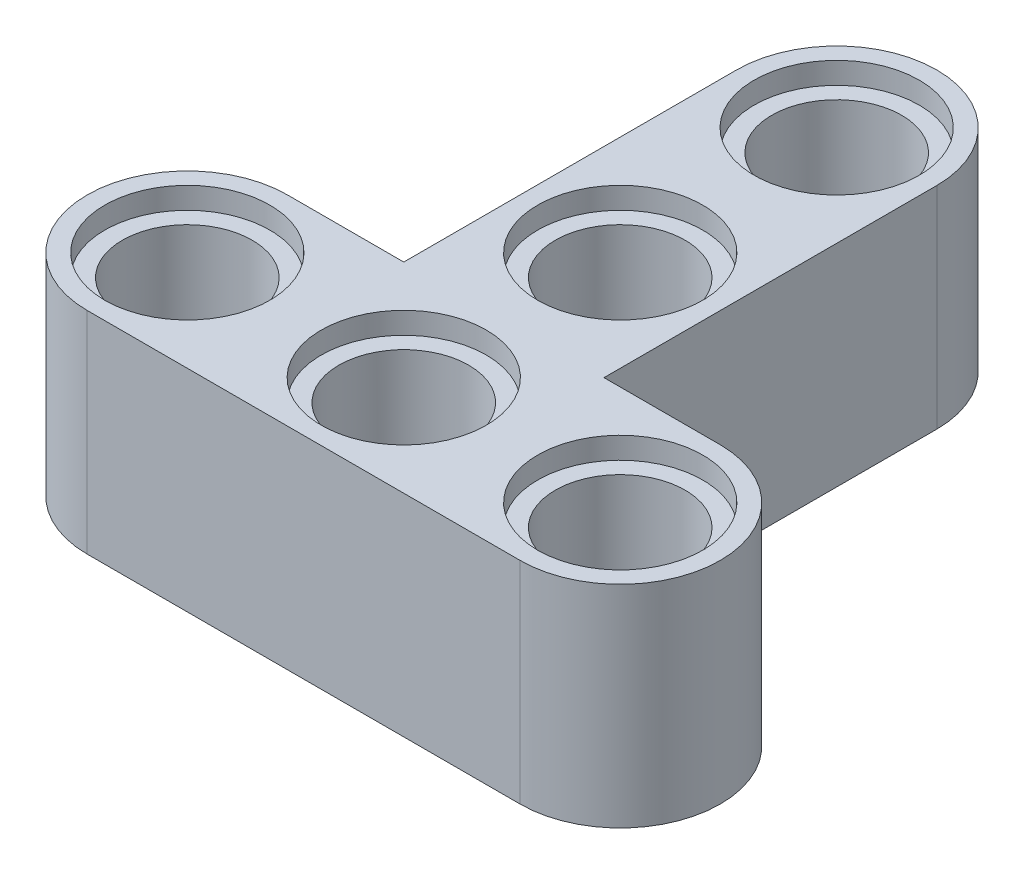
SolidWorks part; units mm, degrees
ref_plane "Front Plane" through (0, 0, 0) normal (0, 0, 1) x (1, 0, 0)
ref_plane "Top Plane" through (0, 0, 0) normal (0, 1, 0) x (1, 0, 0)
ref_plane "Right Plane" through (0, 0, 0) normal (1, 0, 0) x (0, 0, -1)
sketch "Sketch1" plane through (0, 0, 0) normal (0, 1, 0) x (1, 0, 0)
  line L0 (-16, -3.7) -> (0, -3.7)
  line L1 (-16, 3.7) -> (-11.7, 3.7)
  line L3 (-11.7, 16) -> (-11.7, 3.7)
  line L4 (-4.3, 16) -> (-4.3, 3.7)
  line L5 (-4.3, 3.7) -> (0, 3.7)
  arc A9 (0, 3.7) -> (0, -3.7) centre (0, 0) cw
  arc A10 (-16, 3.7) -> (-16, -3.7) centre (-16, 0) ccw
  arc A12 (-4.3, 16) -> (-11.7, 16) centre (-8, 16) ccw
  point P20 (8, -3.7)
  point P25 (-8, -3.7)
  dimension "D1" = 3.7
  dimension "D5" = 3.7
  dimension "D2" = 16
extrude "Boss-Extrude3" add sketch "Sketch1" along normal blind 7.8 contours A10 L0 A9 L5 L4 A12 L3 L1
sketch "Sketch2" plane through (0, 7.8, 0) normal (0, 1, 0) x (1, 0, 0)
  circle A0 centre (0, 0) radius 2.4
  circle A6 centre (-16, 0) radius 2.4
  circle A9 centre (-8, 0) radius 2.4
  circle A10 centre (-8, 8) radius 2.4
  circle A11 centre (-8, 16) radius 2.4
  dimension "D1" = 4.8
  dimension "D2" = 8
  dimension "D3" = 8
sketch "Sketch3" plane through (0, 7.8, 0) normal (0, 1, 0) x (1, 0, 0)
  circle A0 centre (0, 0) radius 3.05
  circle A3 centre (-16, 0) radius 3.05
  circle A4 centre (-8, 0) radius 3.05
  circle A5 centre (-8, 8) radius 3.05
  circle A6 centre (-8, 16) radius 3.05
  dimension "D1" = 6.1
  dimension "D2" = 8
  dimension "D3" = 8
sketch "Sketch4" plane through (0, 0, 0) normal (0, -1, 0) x (1, 0, 0)
  circle A0 centre (0, 0) radius 3.05
  circle A3 centre (-16, 0) radius 3.05
  circle A4 centre (-8, 0) radius 3.05
  circle A5 centre (-8, -16) radius 3.1299
  circle A6 centre (-8, -8) radius 3.05
  dimension "D1" = 6.1
  dimension "D3" = 8
  dimension "D2" = 8
extrude "Cut-Extrude1" cut sketch "Sketch2" against normal blind 7.8
extrude "Cut-Extrude2" cut sketch "Sketch3" against normal blind 0.8
extrude "Cut-Extrude3" cut sketch "Sketch4" against normal blind 0.8
